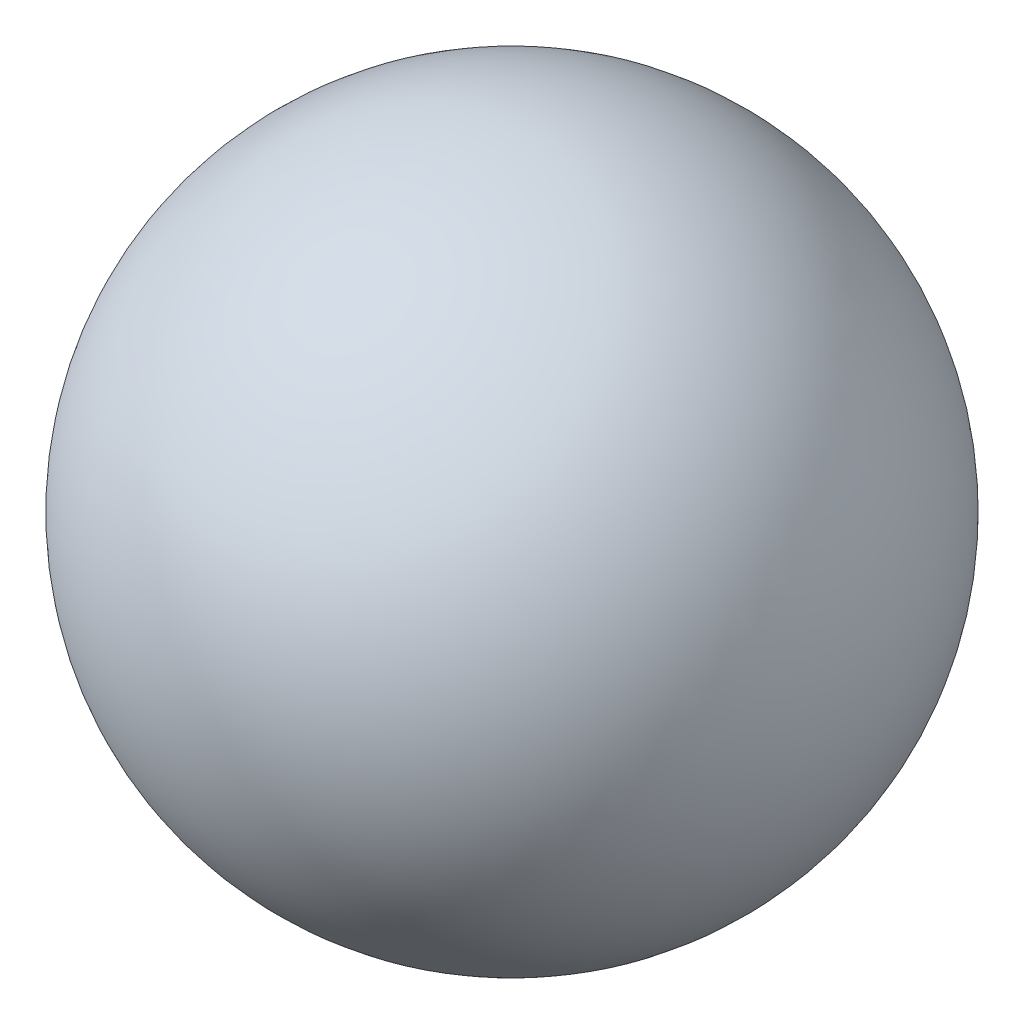
SolidWorks part; units mm, degrees
ref_plane "Front Plane" through (0, 0, 0) normal (0, 0, 1) x (1, 0, 0)
ref_plane "Top Plane" through (0, 0, 0) normal (0, 1, 0) x (1, 0, 0)
ref_plane "Right Plane" through (0, 0, 0) normal (1, 0, 0) x (0, 0, -1)
sketch "Sketch1" plane through (0, 0, 0) normal (0, 0, 1) x (1, 0, 0)
  line L0 (0, -1.0946) -> (0, 1.9054)
  arc A0 (0, -1.0946) -> (0, 1.9054) centre (0, 0.4054) cw
  dimension "D1" = 3
revolve "Revolve1" add sketch "Sketch1" angle 360 about L0
